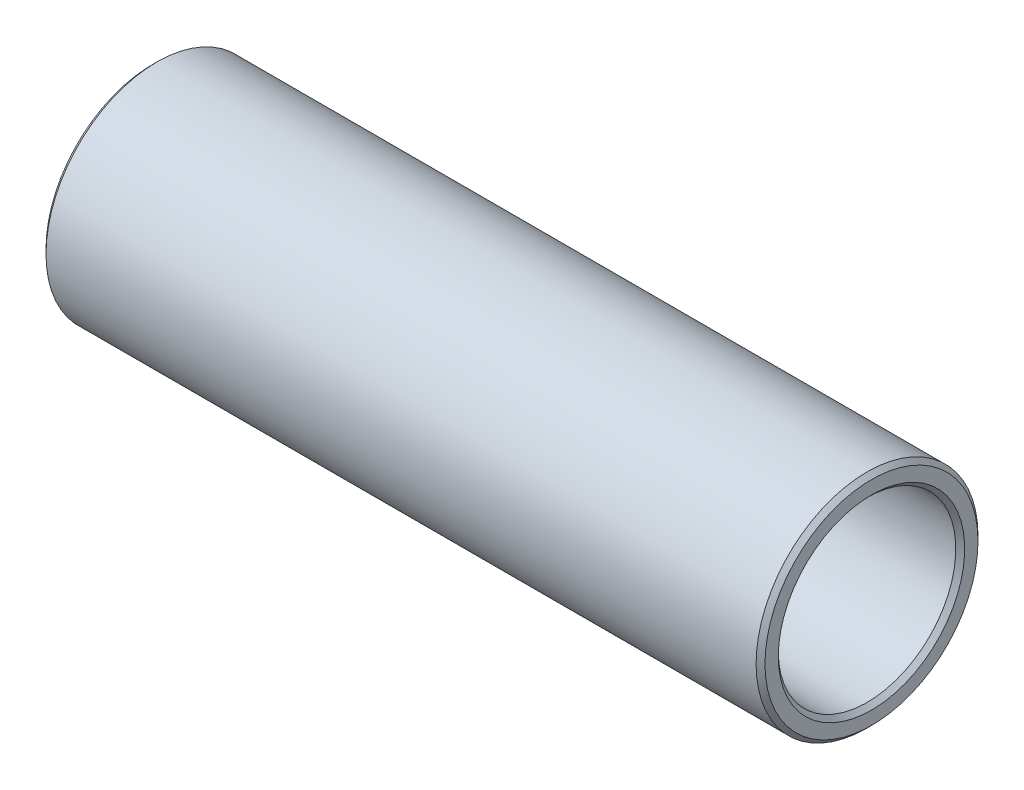
SolidWorks part; units mm, degrees
material "Сталь 40Х ГОСТ 4543-71"
ref_plane "Спереди (Плоскость XY)" through (0, 0, 0) normal (0, 0, 1) x (1, 0, 0)
ref_plane "Сверху (Плоскость XZ)" through (0, 0, 0) normal (0, 1, 0) x (1, 0, 0)
ref_plane "Справа (Плоскость ZY)" through (0, 0, 0) normal (1, 0, 0) x (0, 0, -1)
other "Configuration Table"
sketch "Эскиз1" plane through (0, 0, 0) normal (0, 0, 1) x (1, 0, 0)
  line L0 (0, 0) -> (62.6109, 0) construction
  line L1 (0, 12.5) -> (0, 10)
  line L2 (0, 10) -> (81, 10)
  line L3 (81, 10) -> (81, 12.5)
  line L4 (81, 12.5) -> (0, 12.5)
  point P5 (81, 11.25)
  dimension "D1" = 20
  dimension "D2" = 25
  dimension "D3" = 81
revolve "Повернуть1" add sketch "Эскиз1" angle 360 about L0
chamfer "Фаска1" distance 0.5 angle 45 4 edges at (0, 0, 12.5) (0, 0, 10) (81, 0, 10) (81, 0, 12.5)
